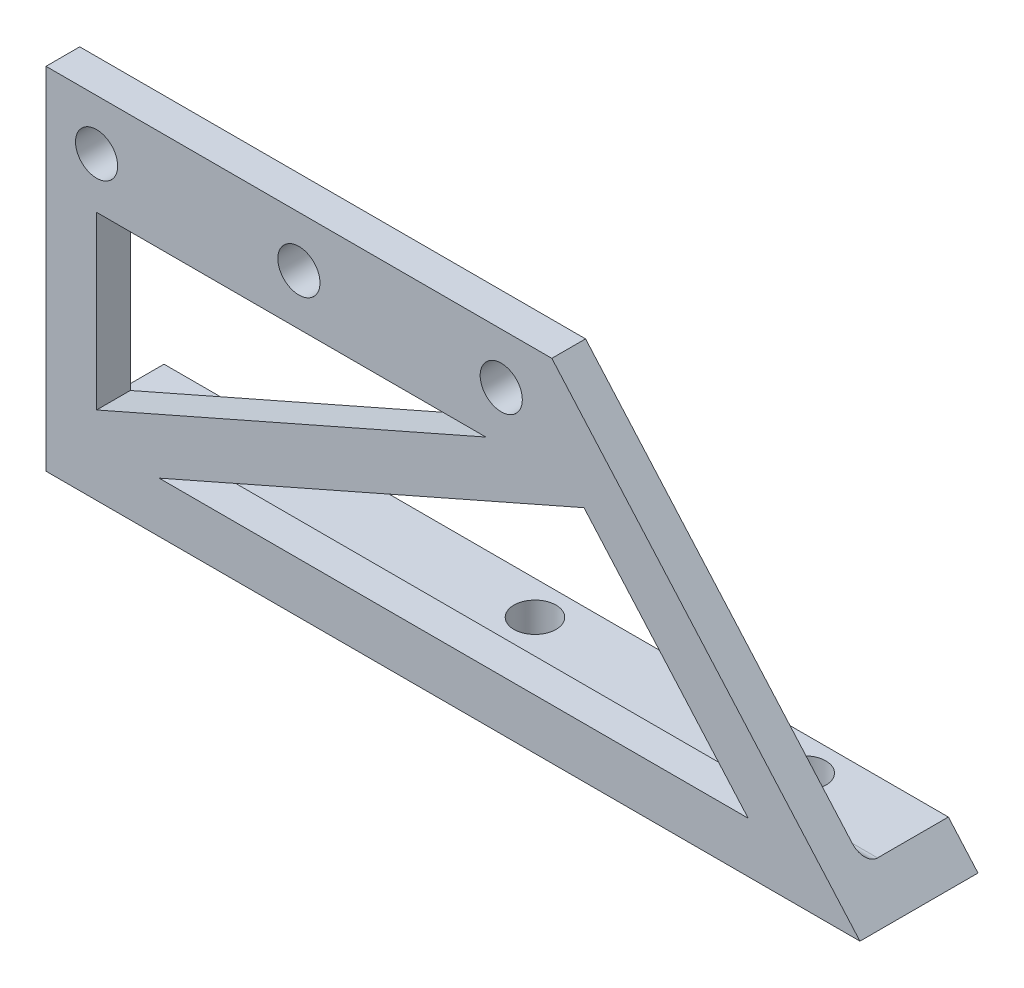
SolidWorks part; units mm, degrees
ref_plane "Front Plane" through (0, 0, 0) normal (0, 0, 1) x (1, 0, 0)
ref_plane "Top Plane" through (0, 0, 0) normal (0, 1, 0) x (1, 0, 0)
ref_plane "Right Plane" through (0, 0, 0) normal (1, 0, 0) x (0, 0, -1)
sketch "Sketch1" plane through (0, 0, 0) normal (0, 0, 1) x (1, 0, 0)
  line L0 (0, 0) -> (0, 66.04)
  line L1 (0, 66.04) -> (95.25, 66.04)
  line L2 (95.25, 66.04) -> (153.2771, 0)
  line L3 (153.2771, 0) -> (0, 0)
  line L4 (9.525, 14.7565) -> (9.525, 46.99)
  line L5 (9.525, 46.99) -> (82.83, 46.99)
  line L6 (82.83, 46.99) -> (9.525, 14.7565)
  line L7 (21.2908, 9.525) -> (101.3112, 44.7114)
  line L8 (101.3112, 44.7114) -> (132.2283, 9.525)
  line L9 (132.2283, 9.525) -> (21.2908, 9.525)
  circle A0 centre (9.525, 56.515) radius 3.9688
  circle A1 centre (47.625, 56.515) radius 3.9687
  circle A2 centre (85.725, 56.515) radius 3.9688
  dimension "D1" = 7.9375
  dimension "D2" = 38.1
  dimension "D3" = 38.1
  dimension "D4" = 9.525
  dimension "D5" = 9.525
  dimension "D6" = 9.525
  dimension "D7" = 9.525
  dimension "D8" = 9.525
  dimension "D9" = 9.525
  dimension "D10" = 56.515
  dimension "D11" = 9.525
extrude "Boss-Extrude1" add sketch "Sketch1" along normal blind 6.35
sketch "Sketch2" plane through (0, 0, 0) normal (0, -1, 0) x (1, 0, 0)
  line L5 (0, 6.35) -> (0, 0) construction
  line L6 (153.2771, 0) -> (0, 0)
  line L7 (153.2771, 0) -> (153.2771, -15.875)
  line L8 (153.2771, -15.875) -> (0, -15.875)
  line L9 (0, 0) -> (0, -15.875)
  circle A0 centre (25.4, -9.525) radius 3.9688
  circle A1 centre (76.2, -9.525) radius 3.9688
  circle A2 centre (127, -9.525) radius 3.9687
  dimension "D4" = 7.9375
  dimension "D1" = 50.8
  dimension "D2" = 50.8
  dimension "D3" = 25.4
  dimension "D5" = 6.35
  dimension "D7" = 15.875
extrude "Boss-Extrude2" add sketch "Sketch2" against normal blind 6.35
fillet "Fillet1" radius 2.54 1 edges
sketch "Sketch3" plane through (0, 0, 0) normal (0, 0, -1) x (-1, 0, 0)
  line L0 (-153.2771, 0) -> (-143.8882, 10.6854)
  line L1 (-145.4658, 8.89) -> (-95.25, 66.04) construction
  line L2 (-143.8882, 10.6854) -> (-163.562, 13.5524)
  line L3 (-163.562, 13.5524) -> (-165.2832, 4.2455)
  line L4 (-165.2832, 4.2455) -> (-153.2771, 0)
extrude "Cut-Extrude1" cut sketch "Sketch3" along normal through all
equation "\"D8@Sketch1\"=\"D6@Sketch1\""
equation "\"D9@Sketch1\"=\"D8@Sketch1\""
equation "\"D5@Sketch2\"=\"D7@Sketch2\"/2*.8"
equation "\"D10@Sketch1\"=3-0.305744in-0.237204in-0.232052in "
